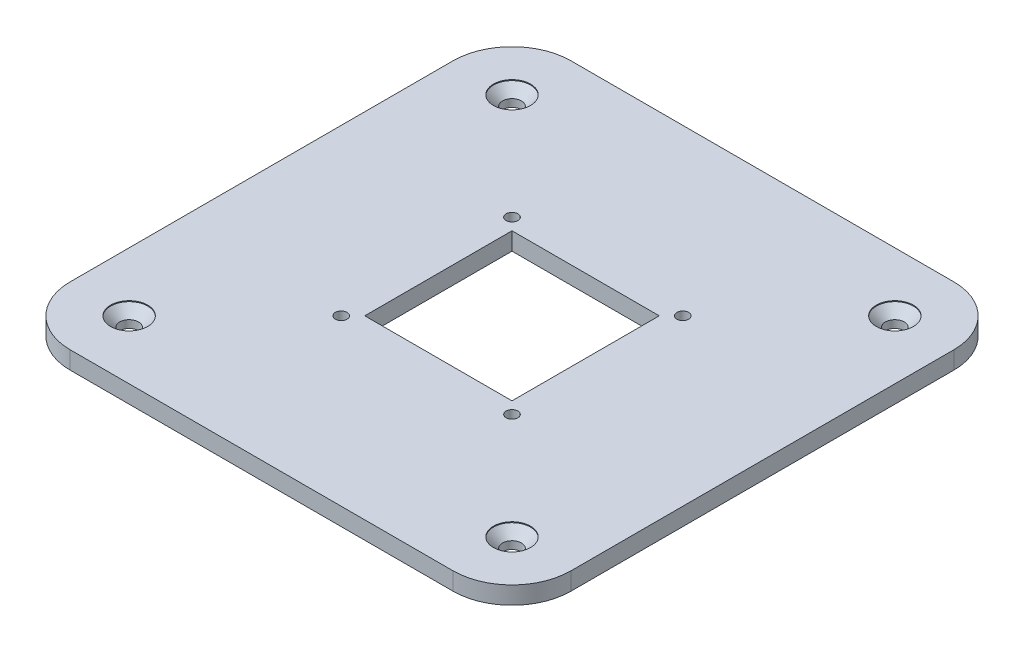
SolidWorks part; units mm, degrees
material "ABS PC"
ref_plane "Front Plane" through (0, 0, 0) normal (0, 0, 1) x (1, 0, 0)
ref_plane "Top Plane" through (0, 0, 0) normal (0, 1, 0) x (1, 0, 0)
ref_plane "Right Plane" through (0, 0, 0) normal (1, 0, 0) x (0, 0, -1)
sketch "Sketch1" plane through (0, 0, 0) normal (0, 1, 0) x (1, 0, 0)
  line L1 (-42.5, -42.5) -> (42.5, -42.5)
  line L2 (-42.5, -42.5) -> (-42.5, 42.5)
  line L3 (-42.5, 42.5) -> (42.5, 42.5)
  line L4 (42.5, -42.5) -> (42.5, 42.5)
  line L5 (-42.5, -42.5) -> (42.5, 42.5) construction
  line L6 (-42.5, 42.5) -> (42.5, -42.5) construction
  point P0 (0, 0)
  dimension "D1" = 85
extrude "Boss-Extrude1" add sketch "Sketch1" along normal blind 3
fillet "Fillet1" radius 10 4 edges at (-42.5, 1.5, -42.5) (42.5, 1.5, -42.5) (42.5, 1.5, 42.5) (-42.5, 1.5, 42.5)
sketch "Sketch3" plane through (0, 3, 0) normal (0, 1, 0) x (1, 0, 0)
  line L1 (-12.5, -12.5) -> (12.5, -12.5)
  line L2 (-12.5, -12.5) -> (-12.5, 12.5)
  line L3 (-12.5, 12.5) -> (12.5, 12.5)
  line L4 (12.5, -12.5) -> (12.5, 12.5)
  line L5 (-12.5, -12.5) -> (12.5, 12.5) construction
  line L6 (-12.5, 12.5) -> (12.5, -12.5) construction
  point P0 (0, 0)
  dimension "D1" = 25
extrude "Cut-Extrude1" cut sketch "Sketch3" against normal up to next
hole_wizard "CSK for M3 Flat Head Machine Screw1" positions "Sketch5" profile "Sketch4" countersink size "M3" standard "ANSI Metric" end condition up to next
sketch "Sketch5" plane through (0, 3, 0) normal (0, 1, 0) x (1, 0, 0)
  point P0 (32.5, 32.5)
  point P2 (32.5, -32.5)
  point P4 (-32.5, -32.5)
  point P6 (-32.5, 32.5)
sketch "Sketch4" plane through (32.5, 3, -32.5) normal (1, 0, 0) x (0, 0, 1)
  line L0 (0, 0) -> (0, 3)
  line L1 (0, 3) -> (1.6, 3)
  line L2 (1.6, 3) -> (1.6, 1.7)
  line L3 (1.6, 1.7) -> (3.15, 0.15)
  line L4 (3.15, 0.15) -> (3.15, 0)
  line L6 (3.15, 0) -> (0, 0)
  line L7 (-1.6, 1.7) -> (-3.15, 0.15) construction
  line L11 (0, -6.35) -> (0, 107.95) construction
  dimension "Thru Hole Dia." = 3.2
  dimension "Thru Hole Depth" = 3
  dimension "C'Sink Dia." = 6.3
  dimension "C'Sink Angle" = 90
  dimension "Head Clearance" = 0.15
sketch "Sketch6" plane through (0, 3, 0) normal (0, 1, 0) x (1, 0, 0)
  circle A0 centre (-14.5, 14.5) radius 1
  circle A1 centre (14.5, 14.5) radius 1
  circle A2 centre (14.5, -14.5) radius 1
  circle A3 centre (-14.5, -14.5) radius 1
  point P12 (0, 0)
  dimension "D1" = 2
  dimension "D2" = 4
extrude "Cut-Extrude2" cut sketch "Sketch6" against normal through all
